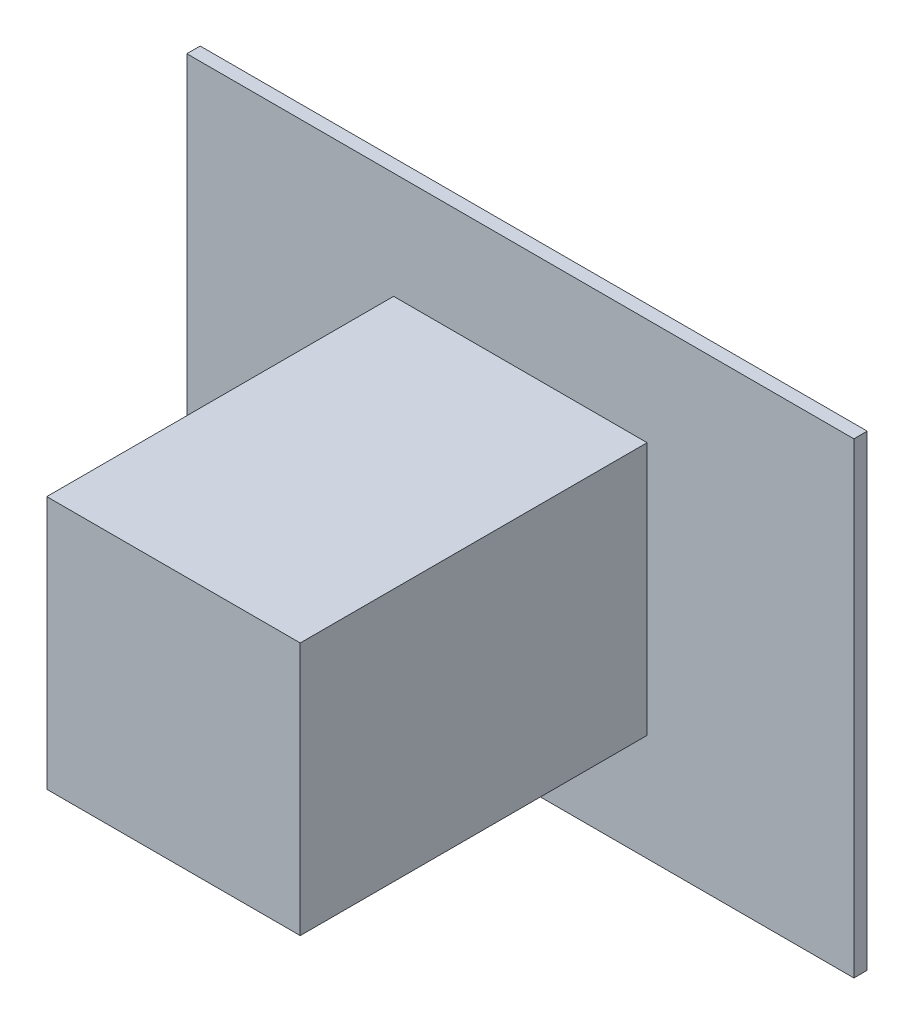
SolidWorks part; units mm, degrees
other "Markup1"
sketch "Sketch5" plane through (2.5, -1.75, 0) normal (0.7329, -0.6618, -0.1577) x (-0.5681, -0.468, -0.6769)
ref_plane "Front Plane" through (0, 0, 0) normal (0, 0, 1) x (1, 0, 0)
ref_plane "Top Plane" through (0, 0, 0) normal (0, 1, 0) x (1, 0, 0)
ref_plane "Right Plane" through (0, 0, 0) normal (1, 0, 0) x (0, 0, -1)
sketch "Sketch1" plane through (0, 0, 0) normal (0, 0, 1) x (1, 0, 0)
  line L1 (0.95, -0.95) -> (-0.95, -0.95)
  line L2 (0.95, -0.95) -> (0.95, 0.95)
  line L3 (0.95, 0.95) -> (-0.95, 0.95)
  line L4 (-0.95, -0.95) -> (-0.95, 0.95)
  line L5 (0.95, -0.95) -> (-0.95, 0.95) construction
  line L6 (0.95, 0.95) -> (-0.95, -0.95) construction
  point P0 (0, 0)
  dimension "D1" = 1.9
  dimension "D2" = 1.9
extrude "Boss-Extrude1" add sketch "Sketch1" along normal blind 3
sketch "Sketch3" plane through (0, 0, 0) normal (1, 0, 0) x (0, 0, -1)
  line L0 (0, 0) -> (0, 0.7)
  line L1 (0, -0.95) -> (0, 0.95) construction
  line L2 (0, 0.7) -> (-0.9722, 0.7)
  line L3 (0, 0) -> (-1.6629, 0)
  arc A0 (-1.6629, 0) -> (-0.9722, 0.7) centre (-0.9629, 0) cw
  dimension "D1" = 0.7
ref_axis "Axis1" through (0, 0, 5.25) along (0, 0, -1)
revolve "Cut-Revolve1" cut sketch "Sketch3" angle 360 about axis through (0, 0, 5.25) along (0, 0, -1)
ref_plane "Plane1" through (0, 0, 0.4) normal (0, 0, -1) x (-1, 0, 0)
sketch "Sketch4" plane through (0, 0, 0.4) normal (0, 0, -1) x (-1, 0, 0)
  line L1 (-2.5, 1.75) -> (2.5, 1.75)
  line L2 (-2.5, 1.75) -> (-2.5, -1.75)
  line L3 (-2.5, -1.75) -> (2.5, -1.75)
  line L4 (2.5, 1.75) -> (2.5, -1.75)
  line L5 (-2.5, 1.75) -> (2.5, -1.75) construction
  line L6 (-2.5, -1.75) -> (2.5, 1.75) construction
  line L7 (0.765, 0.7369) -> (-0.765, 0.7369)
  line L8 (0.765, 0.7369) -> (0.765, -0.7369)
  line L9 (0.765, -0.7369) -> (-0.765, -0.7369)
  line L10 (-0.765, 0.7369) -> (-0.765, -0.7369)
  line L11 (0.765, 0.7369) -> (-0.765, -0.7369) construction
  line L12 (0.765, -0.7369) -> (-0.765, 0.7369) construction
  point P0 (0, 0)
  point P6 (0, 0)
  dimension "D1" = 5
  dimension "D2" = 3.5
extrude "Boss-Extrude2" add sketch "Sketch4" along normal blind 0.1
